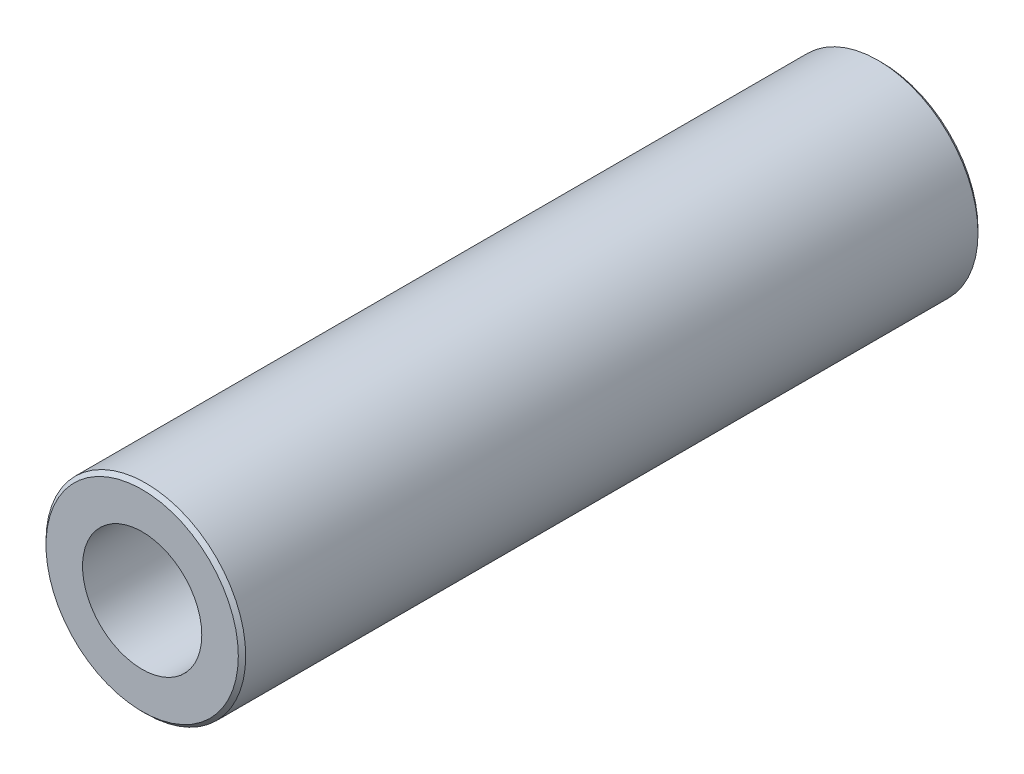
SolidWorks part; units mm, degrees
ref_plane "Front Plane" through (0, 0, 0) normal (0, 0, 1) x (1, 0, 0)
ref_plane "Top Plane" through (0, 0, 0) normal (0, 1, 0) x (1, 0, 0)
ref_plane "Right Plane" through (0, 0, 0) normal (1, 0, 0) x (0, 0, -1)
sketch "Sketch1" plane through (0, 0, 0) normal (0, 1, 0) x (1, 0, 0)
  line L0 (8.255, 0) -> (5.1181, 0)
  line L1 (5.1181, 0) -> (5.1181, -63.5)
  line L2 (5.1181, -63.5) -> (8.255, -63.5)
  line L3 (8.255, -63.5) -> (8.5725, -63.1825)
  line L4 (8.5725, -63.1825) -> (8.5725, -0.3175)
  line L5 (8.5725, -0.3175) -> (8.255, 0)
  line L6 (0, 0) -> (0, -63.5) construction
revolve "Revolve1" add sketch "Sketch1" angle 360 about L6
